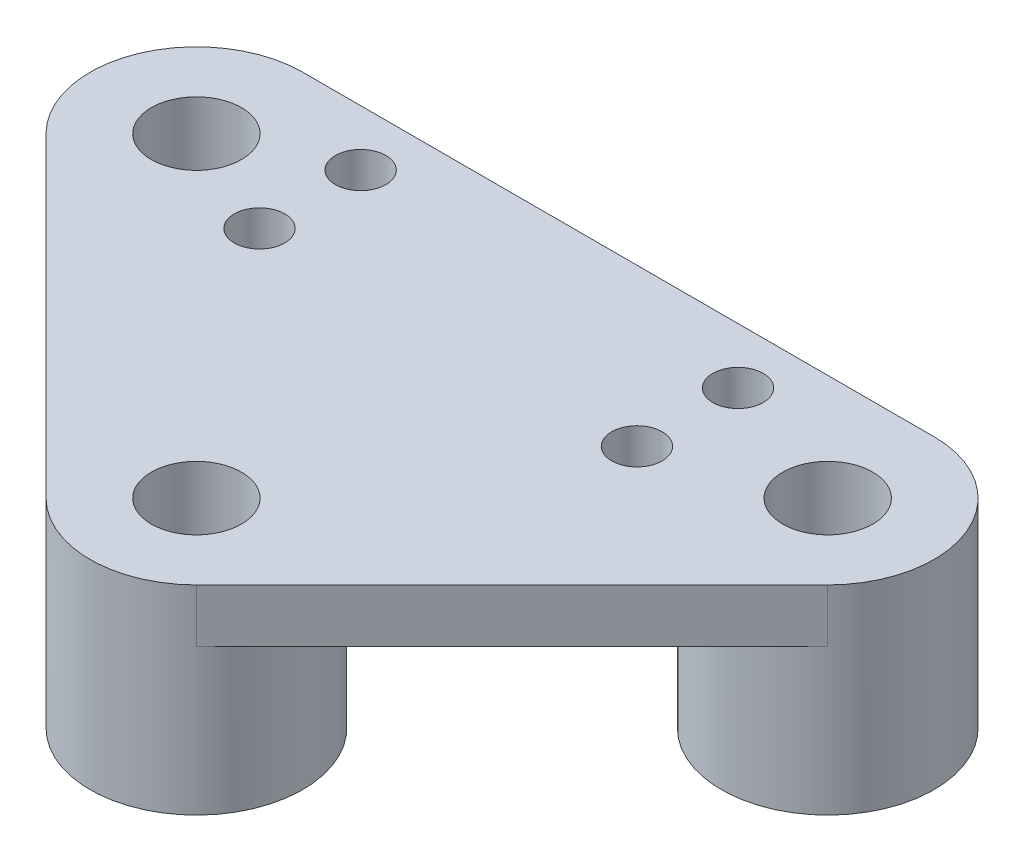
SolidWorks part; units mm, degrees
ref_plane "Front Plane" through (0, 0, 0) normal (0, 0, 1) x (1, 0, 0)
ref_plane "Top Plane" through (0, 0, 0) normal (0, 1, 0) x (1, 0, 0)
ref_plane "Right Plane" through (0, 0, 0) normal (1, 0, 0) x (0, 0, -1)
sketch "Sketch1" plane through (0, 0, 0) normal (0, 1, 0) x (1, 0, 0)
  line L0 (-15.0812, 0) -> (15.0812, 0) construction
  line L1 (-15.0813, 5.08) -> (15.0812, 5.08)
  line L3 (-3.5921, -18.6734) -> (-18.6734, -3.5921)
  line L5 (18.6734, -3.5921) -> (3.5921, -18.6734)
  arc A0 (-15.0813, 5.08) -> (-18.6734, -3.5921) centre (-15.0812, 0) ccw
  arc A1 (18.6734, -3.5921) -> (15.0812, 5.08) centre (15.0812, 0) ccw
  circle A2 centre (0, 0) radius 15.0812 construction
  arc A3 (-3.5921, -18.6734) -> (3.5921, -18.6734) centre (0, -15.0812) ccw
  point P2 (0, 0)
  dimension "D1" = 5.08
  dimension "D2" = 30.1625
extrude "Boss-Extrude1" add sketch "Sketch1" along normal blind 2.54
sketch "Sketch2" plane through (0, 0, 0) normal (0, -1, 0) x (1, 0, 0)
  circle A0 centre (-15.0812, 0) radius 5.08
  circle A1 centre (0, 15.0812) radius 5.08
  circle A2 centre (15.0812, 0) radius 5.08
  arc A3 (3.5921, 18.6734) -> (-3.5921, 18.6734) centre (0, 15.0812) ccw construction
extrude "Boss-Extrude2" add sketch "Sketch2" along normal blind 6.985
hole_wizard "#6 Clearance Hole1" positions "Sketch3" profile "Sketch4" hole size "#6" standard "ANSI Inch" end condition through all
sketch "Sketch3" plane through (0, 2.54, 0) normal (0, 1, 0) x (1, 0, 0)
  point P0 (-15.0812, 0)
  point P3 (0, -15.0812)
  point P6 (15.0812, 0)
sketch "Sketch4" plane through (-15.0812, 2.54, 0) normal (1, 0, 0) x (0, 0, 1)
  line L0 (0, 0) -> (0, 9.525)
  line L1 (0, 9.525) -> (2.1526, 9.525)
  line L2 (2.1526, 9.525) -> (2.1526, 0)
  line L5 (2.1526, 0) -> (0, 0)
  line L11 (0, -6.35) -> (0, 107.95) construction
  dimension "Thru Hole Dia." = 4.3053
  dimension "Thru Hole Depth" = 9.525
hole_wizard "Tap Drill for #4-40 Tap1" positions "Sketch5" profile "Sketch6" hole size "#4-40" standard "ANSI Inch" end condition through all
sketch "Sketch5" plane through (0, 2.54, 0) normal (0, 1, 0) x (1, 0, 0)
  line L1 (8.38, -2.415) -> (-9.65, -2.415) construction
  line L2 (8.38, -2.415) -> (8.38, 2.415) construction
  line L3 (8.38, 2.415) -> (-9.65, 2.415) construction
  line L4 (-9.65, -2.415) -> (-9.65, 2.415) construction
  line L5 (8.38, -2.415) -> (-9.65, 2.415) construction
  line L6 (8.38, 2.415) -> (-9.65, -2.415) construction
  point P0 (8.38, -2.415)
  point P2 (8.38, 2.415)
  point P4 (-9.65, -2.415)
  point P6 (-9.65, 2.415)
  point P36 (-0.635, 0)
  dimension "D1" = 4.83
  dimension "D2" = 18.03
  dimension "D3" = 9.65
sketch "Sketch6" plane through (8.38, 2.54, 2.415) normal (1, 0, 0) x (0, 0, 1)
  line L0 (0, 0) -> (0, 9.525)
  line L1 (0, 9.525) -> (1.2065, 9.525)
  line L2 (1.2065, 9.525) -> (1.2065, 0)
  line L5 (1.2065, 0) -> (0, 0)
  line L11 (0, -6.35) -> (0, 107.95) construction
  dimension "Thru Hole Dia." = 2.413
  dimension "Thru Hole Depth" = 9.525
equation "\"D1@Sketch5\"=4.83mm"
equation "\"D2@Sketch5\"=18.03mm"
equation "\"D3@Sketch5\"=9.65mm"
